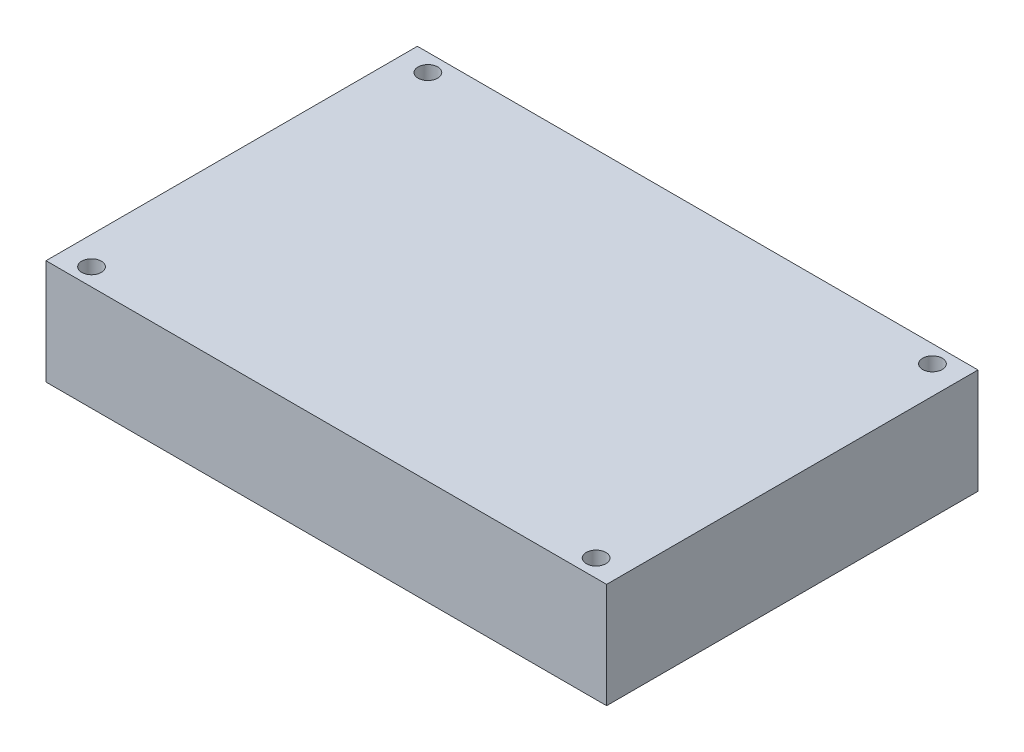
SolidWorks part; units mm, degrees
ref_plane "前视基准面" through (0, 0, 0) normal (0, 0, 1) x (1, 0, 0)
ref_plane "上视基准面" through (0, 0, 0) normal (0, 1, 0) x (1, 0, 0)
ref_plane "右视基准面" through (0, 0, 0) normal (1, 0, 0) x (0, 0, -1)
sketch "草图1" plane through (0, 0, 0) normal (0, 1, 0) x (1, 0, 0)
  line L0 (80, 53) -> (80, 0)
  line L1 (0, 0) -> (0, 53)
  line L2 (0, 53) -> (39.5, 53)
  line L3 (41.5, 53) -> (80, 53)
  line L4 (0, 0) -> (80, 0)
  line L5 (39.5, 53) -> (41.5, 53)
  circle A0 centre (76, 50.5) radius 1.4
  circle A1 centre (76, 2.5) radius 1.4
  circle A2 centre (4, 50.5) radius 1.4
  circle A3 centre (4, 2.5) radius 1.4
extrude "凸台-拉伸1" add sketch "草图1" along normal blind 15
sketch "草图2" plane through (0, 15, 0) normal (0, 1, 0) x (1, 0, 0)
  circle A0 centre (10.5869, 47.7213) radius 1.682
  circle A1 centre (15.5869, 47.7213) radius 1.682
  circle A2 centre (20.5869, 47.7213) radius 1.682
  circle A3 centre (25.5869, 47.7213) radius 1.682
  circle A4 centre (30.5869, 47.7213) radius 1.682
  circle A5 centre (35.5869, 47.7213) radius 1.682
  circle A6 centre (40.5869, 47.7213) radius 1.682
  circle A7 centre (45.5869, 47.7213) radius 1.682
  circle A8 centre (50.5869, 47.7213) radius 1.682
  circle A9 centre (55.5869, 47.7213) radius 1.682
  circle A10 centre (60.5869, 47.7213) radius 1.682
  circle A11 centre (65.5869, 47.7213) radius 1.682
  circle A12 centre (70.5869, 47.7213) radius 1.682
  circle A13 centre (15.5869, 42.7213) radius 1.682
  circle A14 centre (20.5869, 42.7213) radius 1.682
  circle A15 centre (25.5869, 42.7213) radius 1.682
  circle A16 centre (30.5869, 42.7213) radius 1.682
  circle A17 centre (35.5869, 42.7213) radius 1.682
  circle A18 centre (40.5869, 42.7213) radius 1.682
  circle A19 centre (45.5869, 42.7213) radius 1.682
  circle A20 centre (50.5869, 42.7213) radius 1.682
  circle A21 centre (55.5869, 42.7213) radius 1.682
  circle A22 centre (60.5869, 42.7213) radius 1.682
  circle A23 centre (65.5869, 42.7213) radius 1.682
  circle A24 centre (70.5869, 42.7213) radius 1.682
  circle A25 centre (15.5869, 37.7213) radius 1.682
  circle A26 centre (20.5869, 37.7213) radius 1.682
  circle A27 centre (25.5869, 37.7213) radius 1.682
  circle A28 centre (30.5869, 37.7213) radius 1.682
  circle A29 centre (35.5869, 37.7213) radius 1.682
  circle A30 centre (40.5869, 37.7213) radius 1.682
  circle A31 centre (45.5869, 37.7213) radius 1.682
  circle A32 centre (50.5869, 37.7213) radius 1.682
  circle A33 centre (55.5869, 37.7213) radius 1.682
  circle A34 centre (60.5869, 37.7213) radius 1.682
  circle A35 centre (65.5869, 37.7213) radius 1.682
  circle A36 centre (70.5869, 37.7213) radius 1.682
  circle A37 centre (10.5869, 42.7213) radius 1.682
  circle A38 centre (10.5869, 37.7213) radius 1.682
  dimension "D1" = 13
  dimension "D2" = 3
sketch "草图3" plane through (0, 15, 0) normal (0, 1, 0) x (1, 0, 0)
  line L0 (20.5869, 27.5316) -> (20.5869, 13.0839)
  line L1 (12.5869, 29.5316) -> (14.5211, 29.5316)
  line L2 (10.5869, 27.5316) -> (10.5869, 13.0839)
  line L3 (12.5869, 11.0839) -> (14.5211, 11.0839)
  line L4 (16.5211, 27.5316) -> (16.5211, 13.0839)
  line L5 (26.5211, 27.5316) -> (26.5211, 13.0839)
  line L6 (22.5869, 11.0839) -> (24.5211, 11.0839)
  line L7 (22.5869, 29.5316) -> (24.5211, 29.5316)
  line L8 (30.5869, 27.5316) -> (30.5869, 13.0839)
  line L9 (36.5211, 27.5316) -> (36.5211, 13.0839)
  line L10 (32.5869, 11.0839) -> (34.5211, 11.0839)
  line L11 (32.5869, 29.5316) -> (34.5211, 29.5316)
  line L12 (40.5869, 27.5316) -> (40.5869, 13.0839)
  line L13 (46.5211, 27.5316) -> (46.5211, 13.0839)
  line L14 (42.5869, 11.0839) -> (44.5211, 11.0839)
  line L15 (42.5869, 29.5316) -> (44.5211, 29.5316)
  arc A0 (10.5869, 13.0839) -> (12.5869, 11.0839) centre (12.5869, 13.0839) ccw
  arc A1 (14.5211, 11.0839) -> (16.5211, 13.0839) centre (14.5211, 13.0839) ccw
  arc A2 (16.5211, 27.5316) -> (14.5211, 29.5316) centre (14.5211, 27.5316) ccw
  arc A3 (12.5869, 29.5316) -> (10.5869, 27.5316) centre (12.5869, 27.5316) ccw
  arc A4 (24.5211, 11.0839) -> (26.5211, 13.0839) centre (24.5211, 13.0839) ccw
  arc A5 (20.5869, 13.0839) -> (22.5869, 11.0839) centre (22.5869, 13.0839) ccw
  arc A6 (22.5869, 29.5316) -> (20.5869, 27.5316) centre (22.5869, 27.5316) ccw
  arc A7 (26.5211, 27.5316) -> (24.5211, 29.5316) centre (24.5211, 27.5316) ccw
  arc A8 (34.5211, 11.0839) -> (36.5211, 13.0839) centre (34.5211, 13.0839) ccw
  arc A9 (30.5869, 13.0839) -> (32.5869, 11.0839) centre (32.5869, 13.0839) ccw
  arc A10 (32.5869, 29.5316) -> (30.5869, 27.5316) centre (32.5869, 27.5316) ccw
  arc A11 (36.5211, 27.5316) -> (34.5211, 29.5316) centre (34.5211, 27.5316) ccw
  arc A12 (44.5211, 11.0839) -> (46.5211, 13.0839) centre (44.5211, 13.0839) ccw
  arc A13 (40.5869, 13.0839) -> (42.5869, 11.0839) centre (42.5869, 13.0839) ccw
  arc A14 (42.5869, 29.5316) -> (40.5869, 27.5316) centre (42.5869, 27.5316) ccw
  arc A15 (46.5211, 27.5316) -> (44.5211, 29.5316) centre (44.5211, 27.5316) ccw
  dimension "D1" = 2
  dimension "D2" = 4
sketch "草图4" plane through (0, 15, 0) normal (0, 1, 0) x (1, 0, 0)
  line L1 (57.2867, 30.3056) -> (65.672, 30.3056)
  line L2 (57.2867, 30.3056) -> (57.2867, 22.6944)
  line L3 (57.2867, 22.6944) -> (65.672, 22.6944)
  line L4 (65.672, 30.3056) -> (65.672, 22.6944)
  line L5 (53.2875, 16.7601) -> (59.0927, 16.7601)
  line L6 (53.2875, 16.7601) -> (53.2875, 11.7289)
  line L7 (53.2875, 11.7289) -> (59.0927, 11.7289)
  line L8 (59.0927, 16.7601) -> (59.0927, 11.7289)
  line L9 (64.8979, 20.1143) -> (71.6062, 20.1143)
  line L10 (64.8979, 20.1143) -> (64.8979, 14.2445)
  line L11 (64.8979, 14.2445) -> (71.6062, 14.2445)
  line L12 (71.6062, 20.1143) -> (71.6062, 14.2445)
  line L13 (51.8684, 7.9878) -> (71.6062, 7.9878)
  line L14 (51.8684, 7.9878) -> (51.8684, 4.5047)
  line L15 (51.8684, 4.5047) -> (71.6062, 4.5047)
  line L16 (71.6062, 7.9878) -> (71.6062, 4.5047)
